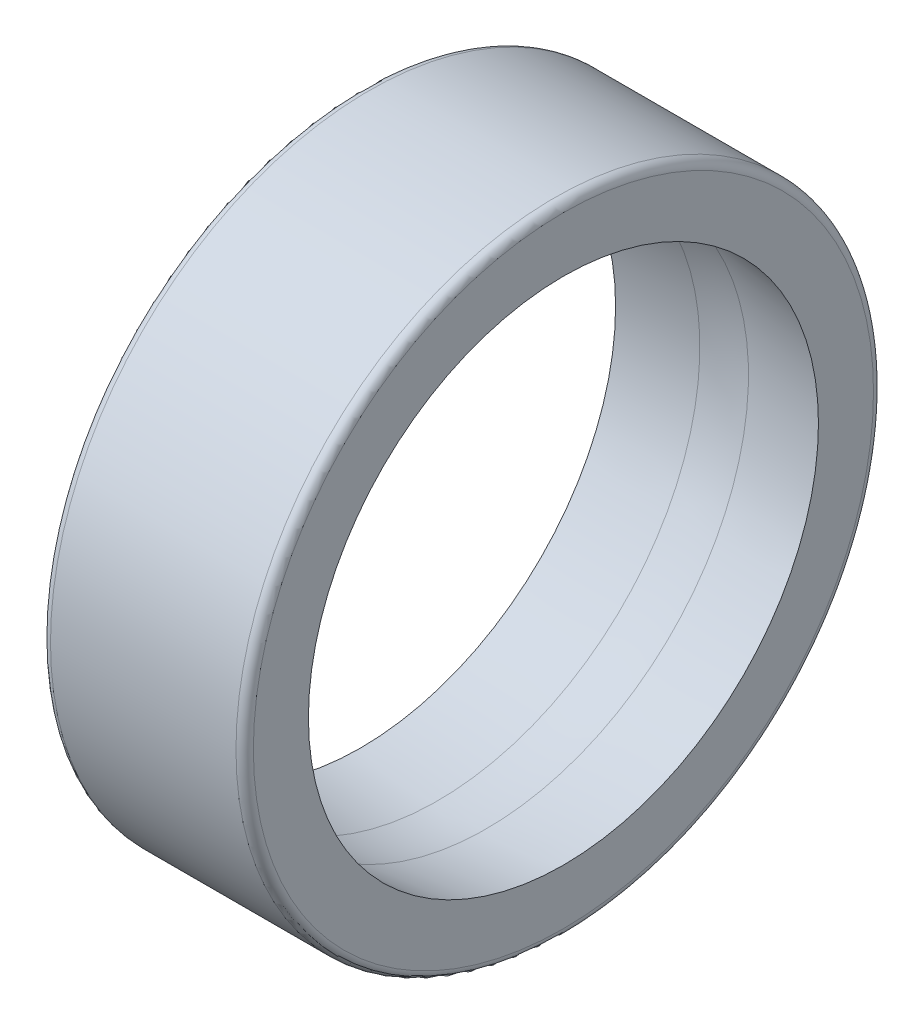
SolidWorks part; units mm, degrees
ref_plane "Front Plane" through (0, 0, 0) normal (0, 0, 1) x (1, 0, 0)
ref_plane "Top Plane" through (0, 0, 0) normal (0, 1, 0) x (1, 0, 0)
ref_plane "Right Plane" through (0, 0, 0) normal (1, 0, 0) x (0, 0, -1)
ref_plane "Plane1" through (0, 0, 0) normal (0, 0, 1) x (1, 0, 0)
sketch "Sketch1" plane through (0, 0, 0) normal (0, 0, 1) x (1, 0, 0)
  line L0 (0, 8.8) -> (2.6612, 9.0467)
  line L1 (4.3388, 9.0467) -> (7, 8.8)
  line L2 (7, 8.8) -> (7, 10.7)
  line L3 (6.7, 11) -> (0.3, 11)
  line L4 (0, 10.7) -> (0, 8.8)
  line L5 (50, 0) -> (-50, 0) construction
  arc A0 (2.6612, 9.0467) -> (4.3388, 9.0467) centre (3.5, 0) cw
  arc A1 (7, 10.7) -> (6.7, 11) centre (6.7, 10.7) ccw
  arc A2 (0.3, 11) -> (0, 10.7) centre (0.3, 10.7) ccw
revolve "Revolve1" add sketch "Sketch1" angle 360 about L5
